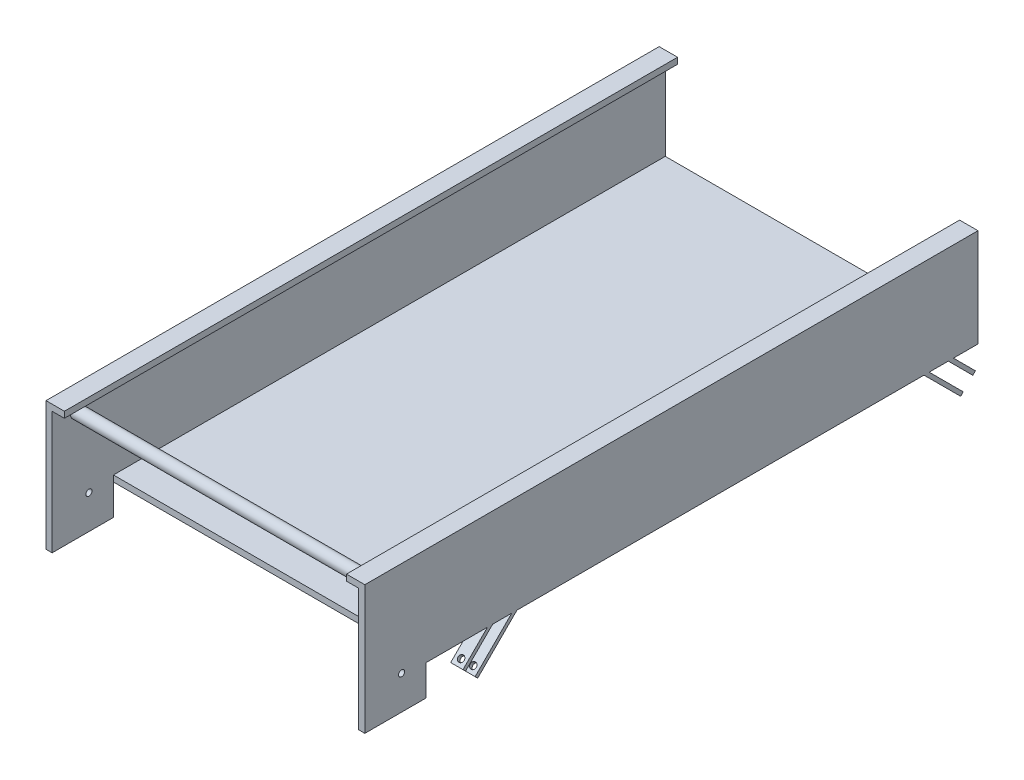
SolidWorks part; units mm, degrees
ref_plane "Front Plane" through (0, 0, 0) normal (0, 0, 1) x (1, 0, 0)
ref_plane "Top Plane" through (0, 0, 0) normal (0, 1, 0) x (1, 0, 0)
ref_plane "Right Plane" through (0, 0, 0) normal (1, 0, 0) x (0, 0, -1)
sketch "Sketch2" plane through (0, 0, 0) normal (0, 0, 1) x (1, 0, 0)
  line L0 (-130, 0) -> (130, 0)
  line L1 (130, 0) -> (130, 80)
  line L2 (130, 80) -> (115, 80)
  line L3 (125, 75) -> (125, 5)
  line L4 (125, 5) -> (-125, 5)
  line L5 (115, 80) -> (115, 75)
  line L6 (115, 75) -> (125, 75)
  line L7 (0, 0) -> (0, 95.8473) construction
  line L8 (-115, 75) -> (-125, 75)
  line L9 (-115, 80) -> (-115, 75)
  line L10 (-125, 75) -> (-125, 5)
  line L11 (-130, 80) -> (-115, 80)
  line L12 (-130, 0) -> (-130, 80)
  point P14 (0, 5)
  dimension "D1" = 130
  dimension "D2" = 125
  dimension "D3" = 70
  dimension "D4" = 5
  dimension "D5" = 5
  dimension "D6" = 10
extrude "Boss-Extrude2" add sketch "Sketch2" along normal blind 500
sketch "Sketch3" plane through (0, 5, 0) normal (0, 1, 0) x (1, 0, 0)
  line L0 (125, -500) -> (125, 0) construction
  line L1 (-125, -500) -> (125, -500)
  line L2 (-125, -500) -> (-125, -450)
  line L3 (-125, -450) -> (125, -450)
  line L4 (125, -500) -> (125, -450)
  dimension "D1" = 50
extrude "Cut-Extrude1" cut sketch "Sketch3" against normal through all
sketch "Sketch5" plane through (125, 0, 0) normal (-1, 0, 0) x (0, 0, 1)
  line L1 (450, 0) -> (500, 0)
  line L2 (450, 0) -> (450, -25)
  line L3 (450, -25) -> (500, -25)
  line L4 (500, 0) -> (500, -25)
  dimension "D1" = 25
extrude "Boss-Extrude3" add sketch "Sketch5" against normal blind 5
sketch "Sketch7" plane through (-125, 0, 0) normal (1, 0, 0) x (0, 0, -1)
  line L0 (-450, 0) -> (-500, 0) construction
  line L1 (-500, 0) -> (-450, 0)
  line L2 (-500, 0) -> (-500, -25)
  line L3 (-500, -25) -> (-450, -25)
  line L4 (-450, 0) -> (-450, -25)
  dimension "D1" = 25
extrude "Boss-Extrude4" add sketch "Sketch7" against normal blind 5
sketch "Sketch8" plane through (125, 0, 0) normal (-1, 0, 0) x (0, 0, 1)
  line L0 (450, 2.5) -> (500, 2.5) construction
  line L1 (450, 0) -> (450, 5) construction
  line L2 (500, 75) -> (500, -25) construction
  line L3 (450, 0) -> (450, -25) construction
  circle A0 centre (470, 2.5) radius 2.5
  dimension "D1" = 5
  dimension "D2" = 20
extrude "Cut-Extrude4" cut sketch "Sketch8" against normal through all both and the other way through all
sketch "Sketch11" plane through (125, 0, 0) normal (-1, 0, 0) x (0, 0, 1)
  line L0 (500, 75) -> (500, -25) construction
  line L1 (500, 75) -> (0, 75) construction
  circle A0 centre (480, 65) radius 5
  dimension "D1" = 20
  dimension "D2" = 10
  dimension "D3" = 10
extrude "Boss-Extrude15" add sketch "Sketch11" along normal blind 250
sketch "Sketch27" plane through (130, 0, 0) normal (1, 0, 0) x (0, 0, -1)
  line L0 (-20, 0) -> (-2.1213, -17.8787)
  line L1 (-450, 0) -> (0, 0) construction
  line L3 (-4.2426, -20) -> (-24.2426, 0)
  line L4 (-24.2426, 0) -> (-20, 0)
  line L5 (-4.2426, -20) -> (-2.1213, -17.8787)
  line L10 (-2.1213, -17.8787) -> (-14.2603, -30.0176) construction
  line L11 (-39.799, 0) -> (-12.0208, -27.7782)
  line L12 (-44.0416, 0) -> (-14.1421, -29.8995)
  line L13 (-44.0416, 0) -> (-39.799, 0)
  line L14 (-14.1421, -29.8995) -> (-12.0208, -27.7782)
  dimension "D1" = 45
  dimension "D2" = 3
  dimension "D3" = 20
  dimension "D4" = 20
  dimension "D6" = 11
  dimension "D5" = 3
extrude "Boss-Extrude16" add sketch "Sketch27" against normal blind 10
sketch "Sketch28" plane through (0, 5, 0) normal (0, 1, 0) x (1, 0, 0)
  line L0 (0, 0) -> (0, -450) construction
  line L1 (125, -450) -> (-125, -450) construction
ref_plane "Plane1" through (0, 0, 0) normal (-1, 0, 0) x (0, 0, 1)
mirror "Mirror1" about plane through (0, 0, 0) normal (-1, 0, 0) of "Boss-Extrude16"
sketch "Sketch29" plane through (130, 0, 0) normal (1, 0, 0) x (0, 0, -1)
  line L0 (-400, 0) -> (-420, -20)
  line L1 (-450, 0) -> (-44.0416, 0) construction
  line L2 (-395.7574, 0) -> (-417.8787, -22.1213)
  line L3 (-420, -20) -> (-417.8787, -22.1213)
  line L4 (-400, 0) -> (-395.7574, 0)
  line L5 (-380.201, 0) -> (-410.1005, -29.8995)
  line L6 (-420, -20) -> (-406.0214, -33.9786) construction
  line L7 (-375.9584, 0) -> (-407.9792, -32.0208)
  line L8 (-380.201, 0) -> (-375.9584, 0)
  line L9 (-410.1005, -29.8995) -> (-407.9792, -32.0208)
  dimension "D1" = 20
  dimension "D2" = 50
  dimension "D3" = 3
  dimension "D4" = 45
  dimension "D5" = 3
  dimension "D6" = 11
extrude "Boss-Extrude17" add sketch "Sketch29" against normal blind 10
mirror "Mirror2" about plane through (0, 0, 0) normal (-1, 0, 0) of "Boss-Extrude17"
sketch "Sketch30" plane through (0, 187.9792, 187.9792) normal (0, -0.7071, -0.7071) x (1, 0, 0)
  line L0 (125, 311.127) -> (125, 265.8427) construction
  line L1 (120, 311.127) -> (130, 311.127) construction
  line L2 (120, 265.8427) -> (130, 265.8427) construction
  circle A0 centre (125, 306.127) radius 2.5
  dimension "D1" = 5
  dimension "D2" = 5
extrude "Cut-Extrude5" cut sketch "Sketch30" against normal up to surface (17 mm away) and the other way through all up to face at (125, -10, 410)
mirror "Mirror3" about plane through (0, 0, 0) normal (-1, 0, 0) of "Cut-Extrude5"
sketch "Sketch31" plane through (0, -22.0208, 22.0208) normal (0, -0.7071, 0.7071) x (1, 0, 0)
  line L0 (125, 31.1421) -> (125, -11.1421) construction
  line L1 (120, 31.1421) -> (130, 31.1421) construction
  line L2 (120, -11.1421) -> (130, -11.1421) construction
  circle A0 centre (125, -6.1421) radius 2.5
  dimension "D1" = 5
  dimension "D2" = 5
extrude "Cut-Extrude6" cut sketch "Sketch31" against normal up to surface (17 mm away) up to face at (125, -8.9393, 11.0607)
mirror "Mirror5" about plane through (0, 0, 0) normal (-1, 0, 0) of "Cut-Extrude6"
